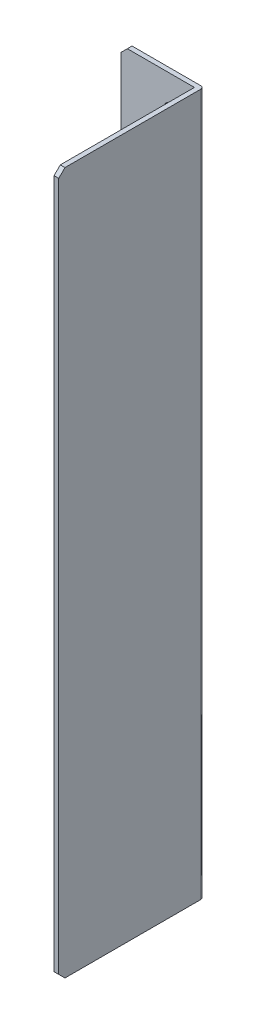
SolidWorks part; units mm, degrees
ref_plane "Front Plane" through (0, 0, 0) normal (0, 0, 1) x (1, 0, 0)
ref_plane "Top Plane" through (0, 0, 0) normal (0, 1, 0) x (1, 0, 0)
ref_plane "Right Plane" through (0, 0, 0) normal (1, 0, 0) x (0, 0, -1)
sketch "Sketch1" plane through (0, 0, 0) normal (0, 0, 1) x (1, 0, 0)
  line L1 (-12.9673, 188.3762) -> (12.0327, 188.3762)
  line L2 (-12.9673, 188.3762) -> (-12.9673, -26.6238)
  line L3 (-7.9673, -36.6238) -> (12.0327, -36.6238)
  line L4 (12.0327, 188.3762) -> (12.0327, -36.6238)
  line L7 (-12.9673, -26.6238) -> (-7.9673, -26.6238)
  line L8 (-7.9673, -36.6238) -> (-7.9673, -26.6238)
  dimension "D1" = 25
  dimension "D2" = 215
  dimension "D3" = 225
  dimension "D4" = 20
extrude "Boss-Extrude1" add sketch "Sketch1" along normal blind 1.5
sketch "Sketch2" plane through (0, 0, 1.5) normal (0, 0, 1) x (1, 0, 0)
  line L0 (12.0327, 188.3762) -> (-12.9673, 188.3762) construction
  line L1 (12.0327, -36.6238) -> (10.5327, -36.6238)
  line L2 (12.0327, -36.6238) -> (12.0327, 188.3762)
  line L3 (12.0327, 188.3762) -> (10.5327, 188.3762)
  line L4 (10.5327, -36.6238) -> (10.5327, 188.3762)
  dimension "D1" = 1.5
extrude "Boss-Extrude2" add sketch "Sketch2" along normal blind 45
chamfer "Chamfer1" distance 2 angle 45 3 edges at (-12.9673, 188.3762, 0.75) (11.2827, 188.3762, 46.5) (11.2827, -36.6238, 46.5)
fillet "Fillet1" radius 1 1 edges at (12.0327, 75.8762, 0)
sketch "Sketch3" plane through (0, 0, 1.5) normal (0, 0, 1) x (1, 0, 0)
  line L0 (12.0327, -34.6238) -> (12.0327, 186.3762) construction
  circle A0 centre (3.0327, 177.9465) radius 2.25
  circle A1 centre (3.0327, -29.0146) radius 2.25
  point P4 (0, 0)
  dimension "D1" = 4.5
  dimension "D2" = 9
extrude "Cut-Extrude1" cut sketch "Sketch3" against normal through all
